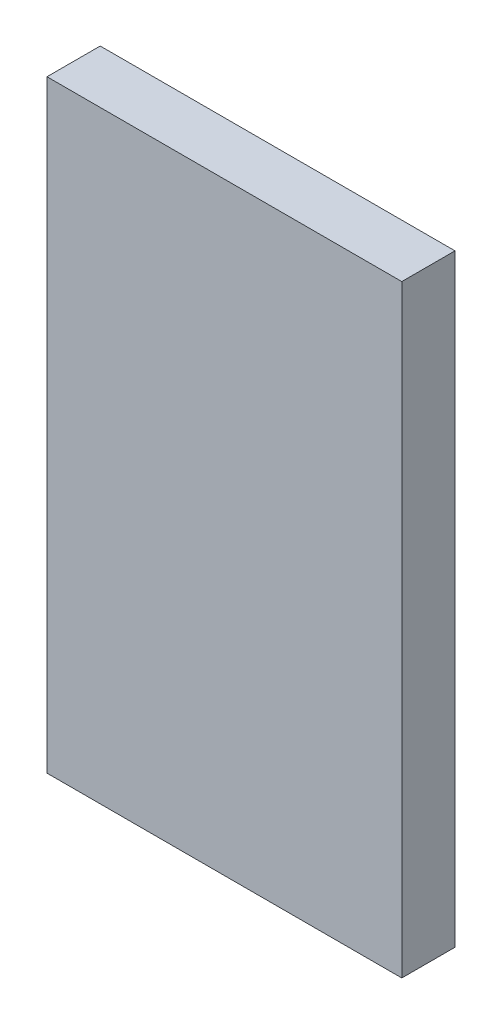
SolidWorks part; units mm, degrees
material "Silicon Rubber"
ref_plane "Front Plane" through (0, 0, 0) normal (0, 0, 1) x (1, 0, 0)
ref_plane "Top Plane" through (0, 0, 0) normal (0, 1, 0) x (1, 0, 0)
ref_plane "Right Plane" through (0, 0, 0) normal (1, 0, 0) x (0, 0, -1)
sketch "Sketch1" plane through (0, 0, 0) normal (0, 0, 1) x (1, 0, 0)
  line L0 (0, 34) -> (0, 0)
  line L1 (0, 34) -> (20, 34)
  line L2 (20, 34) -> (20, 0)
  line L3 (20, 0) -> (0, 0)
  dimension "D1" = 20
  dimension "D2" = 34
extrude "Joint Body" add sketch "Sketch1" along normal blind 3
equation "\"D1@Sketch1\"  = \"Wjoint@Parameters@RobotHandParameters.SLDPRT\""
equation "\"D2@Sketch1\"=\"Ljointp@Parameters@RobotHandParameters.SLDPRT\" + 24"
equation "\"D1@Joint Body\" = \"Tjointp@Parameters@RobotHandParameters.SLDPRT\""
